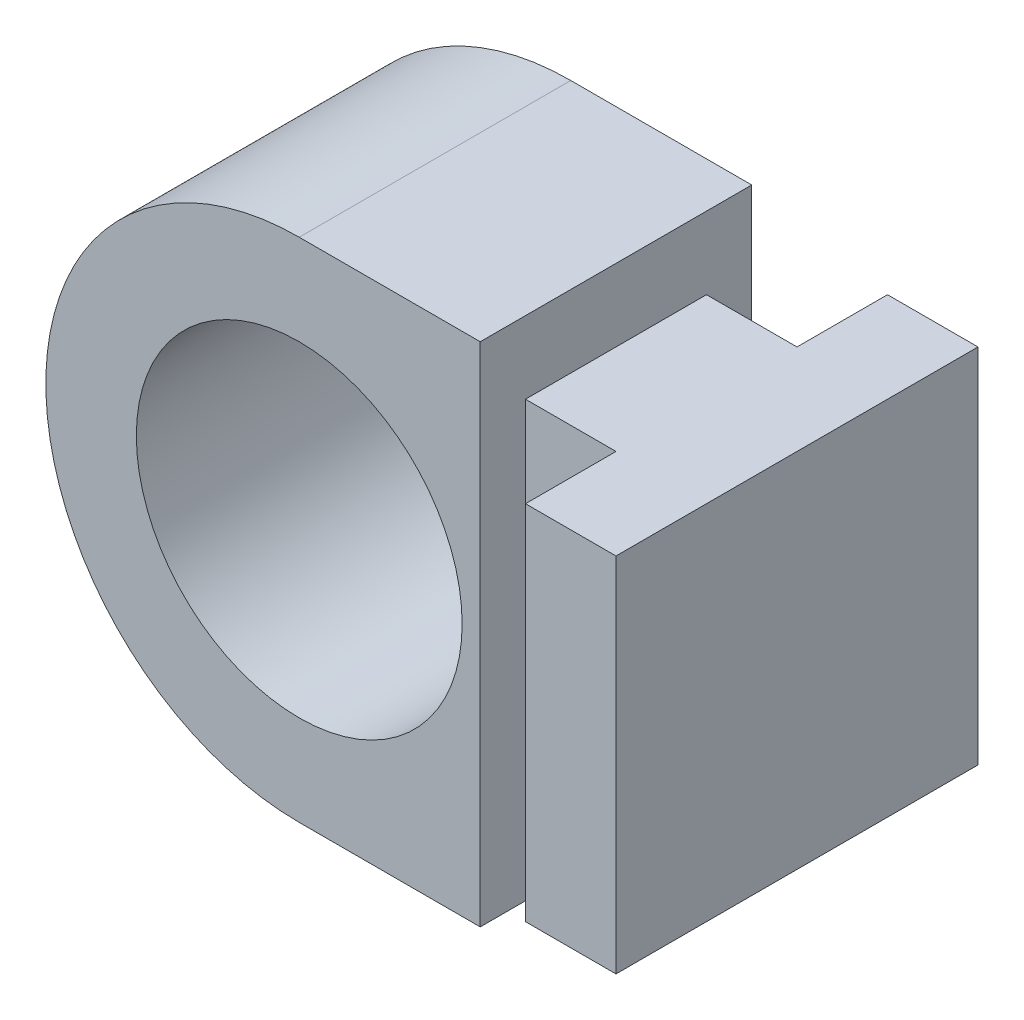
SolidWorks part; units mm, degrees
ref_plane "Front Plane" through (0, 0, 0) normal (0, 0, 1) x (1, 0, 0)
ref_plane "Top Plane" through (0, 0, 0) normal (0, 1, 0) x (1, 0, 0)
ref_plane "Right Plane" through (0, 0, 0) normal (1, 0, 0) x (0, 0, -1)
sketch "Esquisse1" plane through (0, 0, 0) normal (0, 0, 1) x (1, 0, 0)
  line L0 (0, 22.5414) -> (0, -24.96) construction
  line L1 (-19.8325, 0) -> (28.8297, 0) construction
  line L2 (0, 14) -> (10, 14)
  line L3 (10, 14) -> (10, -14)
  line L7 (0, -14) -> (10, -14)
  circle A2 centre (0, 0) radius 9
  arc A3 (0, 14) -> (0, -14) centre (0, 0) ccw
  dimension "D1" = 18
  dimension "D2" = 28
  dimension "D3" = 10
extrude "Boss.-Extru.1" add sketch "Esquisse1" along normal mid plane 15
sketch "Esquisse2" plane through (0, 14, 0) normal (0, 1, 0) x (1, 0, 0)
  line L0 (-12.2734, 0) -> (17.4483, 0) construction
  line L1 (10, 5) -> (15, 5)
  line L2 (10, -7.5) -> (10, 7.5) construction
  line L3 (15, 5) -> (15, 10)
  line L4 (15, 10) -> (20, 10)
  line L5 (15, -10) -> (20, -10)
  line L6 (15, -5) -> (15, -10)
  line L7 (10, -5) -> (15, -5)
  line L8 (20, 10) -> (20, -10)
  line L9 (10, 5) -> (10, -5)
  dimension "D1" = 10
  dimension "D2" = 5
  dimension "D3" = 5
  dimension "D4" = 10
extrude "Boss.-Extru.2" add sketch "Esquisse2" against normal blind 20 from offset 4 separate body
